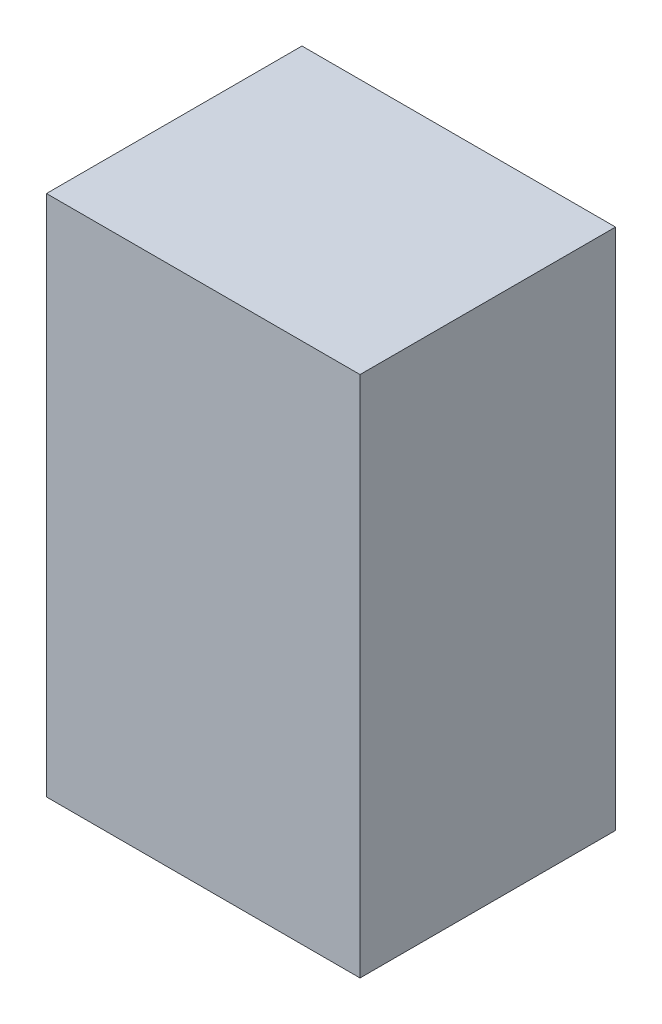
SolidWorks part; units mm, degrees
ref_plane "Front Plane" through (0, 0, 0) normal (0, 0, 1) x (1, 0, 0)
ref_plane "Top Plane" through (0, 0, 0) normal (0, 1, 0) x (1, 0, 0)
ref_plane "Right Plane" through (0, 0, 0) normal (1, 0, 0) x (0, 0, -1)
sketch "Sketch1" plane through (0, 0, 0) normal (0, 0, 1) x (1, 0, 0)
  line L1 (0, 0) -> (54, 0)
  line L2 (0, 0) -> (0, 90)
  line L3 (0, 90) -> (54, 90)
  line L4 (54, 0) -> (54, 90)
  line L5 (8, 82) -> (46, 82)
  line L6 (8, 82) -> (8, 8)
  line L7 (8, 8) -> (46, 8)
  line L8 (46, 82) -> (46, 8)
  dimension "D1" = 90
  dimension "D2" = 54
  dimension "D3" = 8
  dimension "D4" = 8
  dimension "D5" = 8
  dimension "D6" = 8
extrude "Boss-Extrude1" add sketch "Sketch1" along normal blind 40
sketch "Sketch2" plane through (46, 0, 0) normal (-1, 0, 0) x (0, 0, 1)
  line L1 (25.889, 63) -> (22.9445, 68.1)
  line L2 (22.9445, 68.1) -> (17.0555, 68.1)
  line L3 (17.0555, 68.1) -> (14.111, 63)
  line L4 (14.111, 63) -> (17.0555, 57.9)
  line L5 (17.0555, 57.9) -> (22.9445, 57.9)
  line L6 (22.9445, 57.9) -> (25.889, 63)
  line L7 (40, 82) -> (0, 82) construction
  line L8 (0, 8) -> (0, 82) construction
  line L9 (40, 8) -> (0, 8) construction
  line L10 (25.889, 27) -> (22.9445, 32.1)
  line L11 (22.9445, 32.1) -> (17.0555, 32.1)
  line L12 (17.0555, 32.1) -> (14.111, 27)
  line L13 (14.111, 27) -> (17.0555, 21.9)
  line L14 (17.0555, 21.9) -> (22.9445, 21.9)
  line L15 (22.9445, 21.9) -> (25.889, 27)
  line L16 (17.0555, 68.1) -> (22.9445, 57.9) construction
  line L17 (22.9445, 21.9) -> (17.0555, 32.1) construction
  line L18 (17.0555, 57.9) -> (22.9445, 68.1) construction
  circle A0 centre (20, 63) radius 5.1 construction
  circle A1 centre (20, 27) radius 5.1 construction
  dimension "D1" = 19
  dimension "D2" = 20
  dimension "D3" = 10.2
  dimension "D4" = 19
  dimension "D5" = 20
  dimension "D6" = 10.2
extrude "Cut-Extrude1" cut sketch "Sketch2" against normal blind 4.1
sketch "Sketch5" plane through (50.1, 0, 0) normal (-1, 0, 0) x (0, 0, 1)
  line L0 (17.0555, 68.1) -> (22.9445, 57.9) construction
  line L1 (17.0555, 57.9) -> (22.9445, 68.1) construction
  line L2 (17.6329, 22.9) -> (22.3671, 22.9)
  line L3 (24.7343, 63) -> (22.3671, 67.1)
  line L4 (22.3671, 67.1) -> (17.6329, 67.1)
  line L5 (17.6329, 67.1) -> (15.2657, 63)
  line L6 (15.2657, 63) -> (17.6329, 58.9)
  line L7 (17.6329, 58.9) -> (22.3671, 58.9)
  line L8 (22.3671, 58.9) -> (24.7343, 63)
  line L9 (15.2657, 27) -> (17.6329, 22.9)
  line L10 (17.6329, 31.1) -> (15.2657, 27)
  line L11 (22.3671, 31.1) -> (17.6329, 31.1)
  line L12 (24.7343, 27) -> (22.3671, 31.1)
  line L13 (22.3671, 22.9) -> (24.7343, 27)
  circle A0 centre (20, 63) radius 4.1 construction
  dimension "D1" = 8.2
  dimension "D2" = 2
extrude "Cut-Extrude2" cut sketch "Sketch5" against normal blind 0.5
sketch "Sketch6" plane through (8, 0, 0) normal (1, 0, 0) x (0, 0, -1)
  line L0 (-40, 82) -> (0, 82) construction
  line L1 (-14.111, 63) -> (-17.0555, 68.1)
  line L2 (-17.0555, 68.1) -> (-22.9445, 68.1)
  line L3 (-22.9445, 68.1) -> (-25.889, 63)
  line L4 (-25.889, 63) -> (-22.9445, 57.9)
  line L5 (-22.9445, 57.9) -> (-17.0555, 57.9)
  line L6 (-17.0555, 57.9) -> (-14.111, 63)
  line L7 (-14.111, 27) -> (-17.0555, 32.1)
  line L8 (-17.0555, 32.1) -> (-22.9445, 32.1)
  line L9 (-22.9445, 32.1) -> (-25.889, 27)
  line L10 (-25.889, 27) -> (-22.9445, 21.9)
  line L11 (-22.9445, 21.9) -> (-17.0555, 21.9)
  line L12 (-17.0555, 21.9) -> (-14.111, 27)
  line L13 (-40, 82) -> (-40, 8) construction
  line L14 (-40, 8) -> (0, 8) construction
  circle A0 centre (-20, 63) radius 5.1 construction
  circle A1 centre (-20, 27) radius 5.1 construction
  point P9 (-20, 82)
  dimension "D1" = 19
  dimension "D2" = 20
  dimension "D3" = 19
  dimension "D4" = 20
  dimension "D5" = 10.2
  dimension "D6" = 10.2
extrude "Cut-Extrude3" cut sketch "Sketch6" against normal blind 4.1
sketch "Sketch7" plane through (3.9, 0, 0) normal (1, 0, 0) x (0, 0, -1)
  line L1 (-40, 82) -> (0, 82) construction
  line L2 (-40, 82) -> (-40, 8) construction
  circle A0 centre (-20, 63) radius 4.1
  circle A1 centre (-20, 27) radius 4.1
  dimension "D3" = 8.2
  dimension "D1" = 19
  dimension "D2" = 20
  dimension "D4" = 2
extrude "Cut-Extrude4" cut sketch "Sketch7" against normal blind 0.5
sketch "Sketch8" plane through (0, 0, 40) normal (0, 0, 1) x (1, 0, 0)
  line L1 (0, 90) -> (54, 90)
  line L2 (0, 90) -> (0, 0)
  line L3 (0, 0) -> (54, 0)
  line L4 (54, 90) -> (54, 0)
extrude "Boss-Extrude2" add sketch "Sketch8" along normal blind 2
sketch "Sketch9" plane through (0, 0, 0) normal (0, 0, -1) x (-1, 0, 0)
  line L1 (-54, 90) -> (0, 90)
  line L2 (-54, 90) -> (-54, 0)
  line L3 (-54, 0) -> (0, 0)
  line L4 (0, 90) -> (0, 0)
extrude "Boss-Extrude3" add sketch "Sketch9" along normal blind 2
